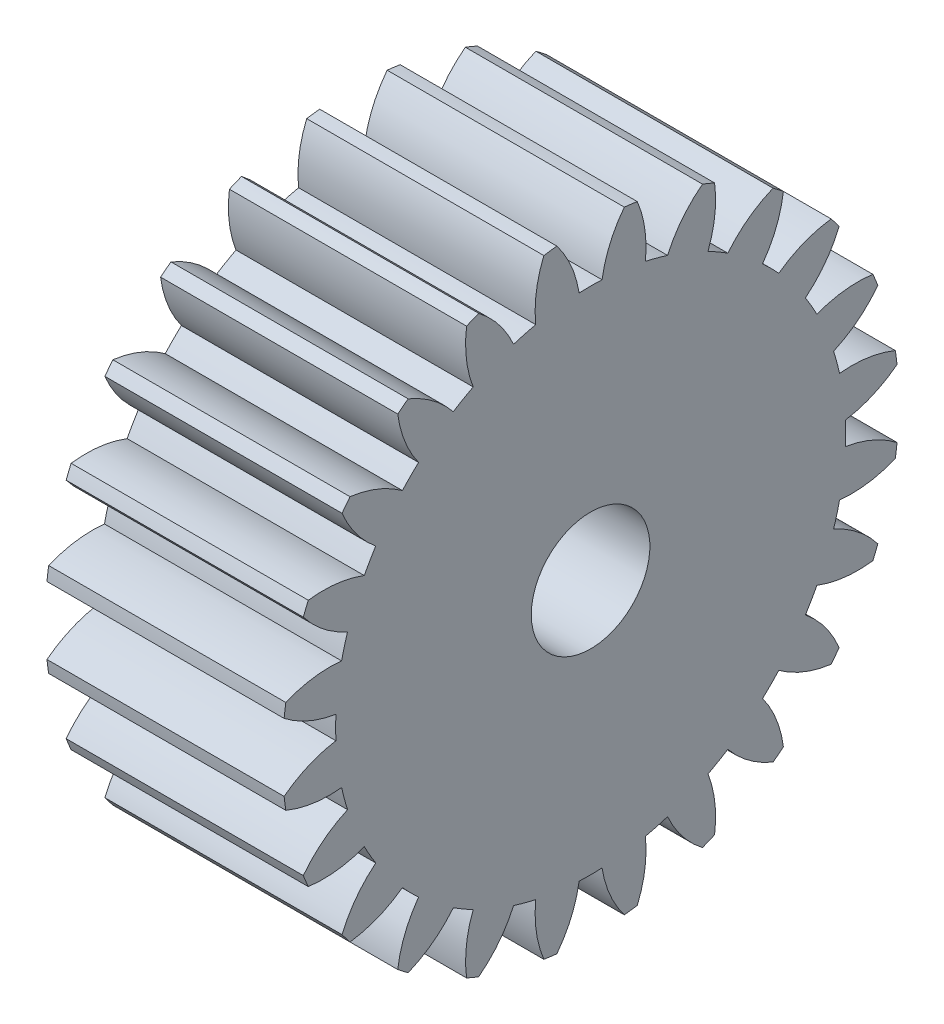
SolidWorks part; units mm, degrees
ref_plane "Plane1" through (0, 0, 0) normal (0, 0, 1) x (1, 0, 0)
ref_plane "Plane2" through (0, 0, 0) normal (0, 1, 0) x (1, 0, 0)
ref_plane "Plane3" through (0, 0, 0) normal (1, 0, 0) x (0, 0, -1)
other "Configuration Table"
sketch "HoldingSke" plane through (0, 0, 0) normal (0, 1, 0) x (1, 0, 0)
  line L0 (0, 0) -> (0.9135, -0.4067)
  line L1 (-15, 0) -> (100, 0) construction
  line L2 (0, 0) -> (-2.1039, 2.3779)
  line L3 (0, 0) -> (-11.863, 4.5341)
  line L4 (0, 0) -> (7.8894, 3.5126)
  line L5 (0, 0) -> (-46.8476, -17.4728)
  line L6 (0, 0) -> (-8.2896, -5.593)
  line L7 (-2.1039, 2.3779) -> (8.6586, 51.2059)
  line L8 (-76.2, 54.61) -> (-75.3, 54.61)
  line L9 (-71.009, 38.7566) -> (-53.1078, 45.2721)
  line L10 (-76.2, 71.12) -> (104.1128, 71.12)
  line L11 (0, 0) -> (-10, 0)
  line L12 (-76.2, 101.6) -> (-76.162, 101.6)
  line L13 (24.9733, 27.94) -> (52.9518, 28.4284)
  line L14 (24.9733, 27.94) -> (24.9743, 27.94)
  line L15 (24.9733, 27.94) -> (100.4006, 29.5858)
  line L16 (-63.627, -1) -> (-12.827, -1)
  circle A0 centre (0, 0) radius 2.5
  circle A1 centre (0, 0) radius 10.749
  circle A2 centre (0, 0) radius 37.5
  circle A3 centre (0, 0) radius 2.5
  dimension "MHD" = 21.498
  dimension "Hub_dia" = 75
  dimension "Bore" = 5
  dimension "MBD" = 5
  dimension "Num_teeth" = 24
  dimension "Pitch" = 1
  dimension "Overall_len" = 50
  dimension "Show_teeth" = 24
  dimension "Thickness" = 10
  dimension "OAL" = 50.0001
  dimension "T_dim" = 0.9
  dimension "Ap" = 20
  dimension "H" = 19.05
  dimension "Pitch_radius" = 180.3128
  dimension "Width" = 10
  dimension "Backlash" = 0.038
  dimension "Addendum_fac" = 1
  dimension "Dedendum_fac" = 1.25
  dimension "Clearance_fac" = 0.25
  dimension "Dedendum_add" = 0.001
  dimension "Module" = 1
sketch "BasProSke" plane through (0, 0, 0) normal (0, 1, 0) x (1, 0, 0)
  line L0 (-10, 0) -> (60, 0) construction
  line L1 (0, 0) -> (0, 13)
  line L2 (0, 0) -> (10, 0)
  line L3 (10, 0) -> (10, 13)
  line L4 (10, 13) -> (0, 13)
  dimension "Thickness" = 10
  dimension "Diameter" = 26
revolve "Base-Revolve" add sketch "BasProSke" angle 360 about L0
sketch "TooCutSke" plane through (0, 0, 0) normal (1, 0, 0) x (0, 0, -1)
  line L1 (0, 0) -> (0, 107) construction
  line L2 (0, 0) -> (-0.8513, 11.9698) construction
  line L3 (0, 0) -> (-3.127, 23.752) construction
  line L4 (-0.8513, 11.9698) -> (-1.5635, 11.876) construction
  arc A0 (0.4834, 10.7381) -> (-0.4834, 10.7381) centre (0, 0) ccw
  arc A1 (1.4409, 12.9455) -> (-1.4409, 12.9455) centre (0, 0) ccw
  circle A2 centre (0, 0) radius 12 construction
  circle A3 centre (0, 0) radius 11.2763 construction
  arc A4 (-0.4834, 10.7381) -> (-1.4409, 12.9455) centre (-5.2252, 9.9926) ccw
  arc A5 (1.4409, 12.9455) -> (0.4834, 10.7381) centre (5.2252, 9.9926) ccw
  dimension "Root_dia" = 21.498
  dimension "Overcut_dia" = 26.0508
  dimension "Pitch_dia" = 24
  dimension "Base_dia" = 22.5526
  dimension "Flank_rad" = 4.8
  dimension "Half_ang" = 7.5
  dimension "Half_CT" = 0.7183
extrude "ToothCut" cut sketch "TooCutSke" along normal through all
fillet "Breaks" [suppressed] radius 0.02
fillet "RootFillets" [suppressed] radius 0.251
pattern_circular "TeethCuts" count 24 every 15 about axis through (-10, 0, 0) along (1, 0, 0) of "ToothCut", "RootFillets", "Breaks"
sketch "HubNeaOneSke" plane through (0, 0, 0) normal (-1, 0, 0) x (0, 0, 1)
  circle A0 centre (0, 0) radius 10.749
  dimension "Diameter" = 21.498
extrude "HubNearOne" [suppressed] add sketch "HubNeaOneSke" along normal blind 40.0001
sketch "HubNeaBotSke" plane through (0, 0, 0) normal (-1, 0, 0) x (0, 0, 1)
  circle A0 centre (0, 0) radius 10.749
  dimension "Diameter" = 21.498
extrude "HubNearBoth" [suppressed] add sketch "HubNeaBotSke" along normal blind 20
ref_plane "FarPln" through (10, 0, 0) normal (1, 0, 0) x (0, 0, -1)
sketch "HubFarSke" plane through (10, 0, 0) normal (1, 0, 0) x (0, 0, -1)
  circle A0 centre (0, 0) radius 10.749
  dimension "Diameter" = 21.498
extrude "HubFar" [suppressed] add sketch "HubFarSke" along normal blind 20
sketch "BorSke" plane through (0, 0, 0) normal (1, 0, 0) x (0, 0, -1)
  circle A0 centre (0, 0) radius 2.5
  dimension "Diameter" = 5
extrude "Bore" cut sketch "BorSke" along normal mid plane 100.0001
sketch "KeySke" plane through (0, 0, 0) normal (1, 0, 0) x (0, 0, -1)
  line L0 (-1, 0) -> (-1, 3.4)
  line L1 (-1, 3.4) -> (1, 3.4)
  line L2 (1, 3.4) -> (1, 0)
  line L3 (0, 0) -> (0, 34) construction
  line L4 (-1, 0) -> (1, 0)
  dimension "Offset" = 3.4
  dimension "Width" = 2
extrude "Keyway" [suppressed] cut sketch "KeySke" along normal mid plane 100.0001
pattern_circular "Keyway2" [suppressed] count 2 every 90 about axis through (-10, 0, 0) along (1, 0, 0)
equation "' \"Module@HoldingSke\" = 6.35"
equation "' \"Num_teeth@HoldingSke\" = 12"
equation "' \"Ap@HoldingSke\" =  20"
equation "' \"Ap@HoldingSke\" = 20"
equation "' \"Width@HoldingSke\" = 0.5 * 25.4"
equation "' \"Hub_dia@HoldingSke\"= 1 * 25.4"
equation "' \"Hub_dia@HoldingSke\" = 1 * 25.4"
equation "' \"Overall_len@HoldingSke\" = 1.0 * 25.4"
equation "' \"Bore@HoldingSke\" = 0.75 * 25.4"
equation "' \"T_dim@HoldingSke\" = 0.1 * 25.4"
equation "' \"Width@KeySke\" = 0.25 * 25.4"
equation "' \"Show_teeth@HoldingSke\" = 13"
equation "' \"Backlash@HoldingSke\" = 0.009 * 25.4"
equation "' \"Addendum_fac@HoldingSke\" = 1.0"
equation "' \"Dedendum_fac@HoldingSke\" = 1.25"
equation "' \"Dedendum_add@HoldingSke\" = 0.00005 * 25.4"
equation "' \"Clearance_fac@HoldingSke\" = 0.25"
equation "\"Pitch@HoldingSke\" = 1 / \"Module@HoldingSke\""
equation "\"Overcut_dia@TooCutSke\" = (\"Num_teeth@HoldingSke\" + 2 * \"Addendum_fac@HoldingSke\") / \"Pitch@HoldingSke\" + 0.002 * 25.4"
equation "\"Pitch_dia@TooCutSke\" = \"Num_teeth@HoldingSke\" / \"Pitch@HoldingSke\""
equation "\"Base_dia@TooCutSke\" = \"Num_teeth@HoldingSke\" / \"Pitch@HoldingSke\" * cos((\"Ap@HoldingSke\"  * 3.14159265 / 180))"
equation "\"Root_dia@TooCutSke\" = (\"Num_teeth@HoldingSke\" + 2) / \"Pitch@HoldingSke\" - 2 * (\"Addendum_fac@HoldingSke\" + \"Dedendum_fac@HoldingSke\") / \"Pitch@HoldingSke\" - \"Dedendum_add@HoldingSke\" * 2"
equation "\"Half_ang@TooCutSke\" = 180 / \"Num_teeth@HoldingSke\""
equation "\"Half_CT@TooCutSke\" = \"Num_teeth@HoldingSke\" / \"Pitch@HoldingSke\" * sin((3.14159265 / 2 / \"Num_teeth@HoldingSke\")) / 2 - 7 * \"Backlash@HoldingSke\" / 4"
equation "\"Flank_rad@TooCutSke\" = \"Num_teeth@HoldingSke\" / \"Pitch@HoldingSke\" / 5"
equation "\"Radius@RootFillets\" = \"Clearance_fac@HoldingSke\" / \"Pitch@HoldingSke\" + \"Dedendum_add@HoldingSke\""
equation "\"Break_rad@Breaks\" = 0.02 / \"Pitch@HoldingSke\""
equation "\"Thickness@HoldingSke\" = \"Width@HoldingSke\""
equation "\"OAL@HoldingSke\" = \"Thickness@HoldingSke\""
equation "\"MHD@HoldingSke\" = (\"Num_teeth@HoldingSke\" + 2) / \"Pitch@HoldingSke\" - 2 * (\"Addendum_fac@HoldingSke\" + \"Dedendum_fac@HoldingSke\")  / \"Pitch@HoldingSke\" - \"Dedendum_add@HoldingSke\" * 2"
equation "\"MBD@HoldingSke\" = (\"Num_teeth@HoldingSke\" + 2) / \"Pitch@HoldingSke\" - 2 * (\"Addendum_fac@HoldingSke\" + \"Dedendum_fac@HoldingSke\")  / \"Pitch@HoldingSke\" - \"Dedendum_add@HoldingSke\" * 2 - 0.002 * 25.4"
equation "\"MHD@HoldingSke\" = ((sgn( \"MHD@HoldingSke\" - \"Hub_dia@HoldingSke\" )-1)*( \"MHD@HoldingSke\" - \"Hub_dia@HoldingSke\" ))/-2+ \"Hub_dia@HoldingSke\""
equation "\"MBD@HoldingSke\" = ((sgn( \"MBD@HoldingSke\" - \"Bore@HoldingSke\" )-1)*( \"MBD@HoldingSke\" - \"Bore@HoldingSke\" ))/-2+ \"Bore@HoldingSke\""
equation "\"OAL@HoldingSke\" = ((sgn( \"OAL@HoldingSke\" - \"Overall_len@HoldingSke\" )+1)*( \"OAL@HoldingSke\" - \"Overall_len@HoldingSke\" ))/2 + \"Overall_len@HoldingSke\" + 0.000002 * 25.4"
equation "\"Num_teeth@TeethCuts\" = int( \"Show_teeth@HoldingSke\" ) + 1"
equation "\"Num_teeth@TeethCuts\" = ((sgn( \"Num_teeth@TeethCuts\" - \"Num_teeth@HoldingSke\" )-1)*( \"Num_teeth@TeethCuts\" - \"Num_teeth@HoldingSke\" ))/-2+ \"Num_teeth@HoldingSke\""
equation "\"Num_teeth@TeethCuts\" = ((sgn( \"Num_teeth@TeethCuts\" - 2.0)+1)*( \"Num_teeth@TeethCuts\" - 2.0))/2 +2.0"
equation "\"Angle@TeethCuts\" = 360.0 / \"Num_teeth@HoldingSke\""
equation "\"Diameter@BasProSke\" = (\"Num_teeth@HoldingSke\" + 2 * \"Addendum_fac@HoldingSke\") / \"Pitch@HoldingSke\""
equation "\"Thickness@BasProSke\"  = \"Thickness@HoldingSke\""
equation "' \"Fillet_rad@BasProSke\" =  \"Thickness@HoldingSke\" * 0.05"
equation "' \"Fillet_rad@BasProSke\" = \"Thickness@HoldingSke\" * 0.05"
equation "\"MHD@HoldingSke\" = ((sgn( \"MHD@HoldingSke\" - \"Root_dia@TooCutSke\" )-1)*( \"MHD@HoldingSke\" - \"Root_dia@TooCutSke\" ))/-2+ \"Root_dia@TooCutSke\""
equation "\"Diameter@HubNeaOneSke\" = \"MHD@HoldingSke\""
equation "\"Length@HubNearOne\" = \"OAL@HoldingSke\" - \"Thickness@BasProSke\""
equation "\"Diameter@HubNeaBotSke\" = \"MHD@HoldingSke\""
equation "\"Length@HubNearBoth\" = ( \"OAL@HoldingSke\" - \"Thickness@BasProSke\" ) / 2.0"
equation "\"Thickness@FarPln\" = \"Thickness@BasProSke\""
equation "\"Diameter@HubFarSke\" = \"MHD@HoldingSke\""
equation "\"Length@HubFar\" = ( \"OAL@HoldingSke\" - \"Thickness@BasProSke\" ) / 2.0"
equation "\"Diameter@BorSke\" = \"MBD@HoldingSke\""
equation "\"D1@Bore\" = \"OAL@HoldingSke\" * 2.0"
equation "\"D1@Keyway\" = \"OAL@HoldingSke\" * 2.0"
equation "\"Offset@KeySke\" = \"T_dim@HoldingSke\" + \"MBD@HoldingSke\" / 2.0"
